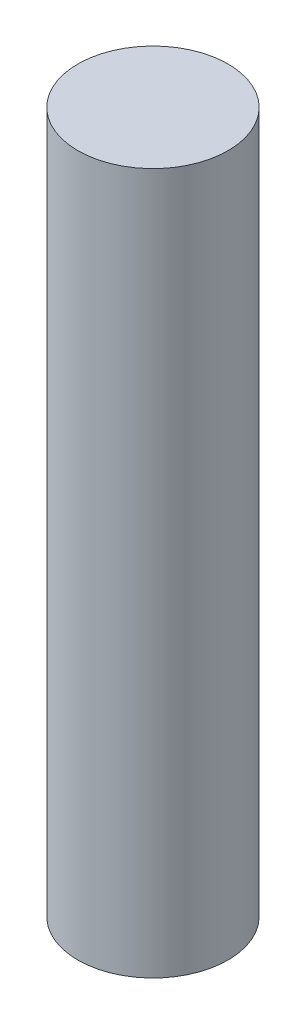
SolidWorks part; units mm, degrees
ref_plane "Front Plane" through (0, 0, 0) normal (0, 0, 1) x (1, 0, 0)
ref_plane "Top Plane" through (0, 0, 0) normal (0, 1, 0) x (1, 0, 0)
ref_plane "Right Plane" through (0, 0, 0) normal (1, 0, 0) x (0, 0, -1)
sketch "Sketch1" plane through (0, 0, 0) normal (0, 1, 0) x (1, 0, 0)
  circle A0 centre (0, 0) radius 9.525
  dimension "D1" = 19.05
extrude "Boss-Extrude1" add sketch "Sketch1" along normal blind 88.9
